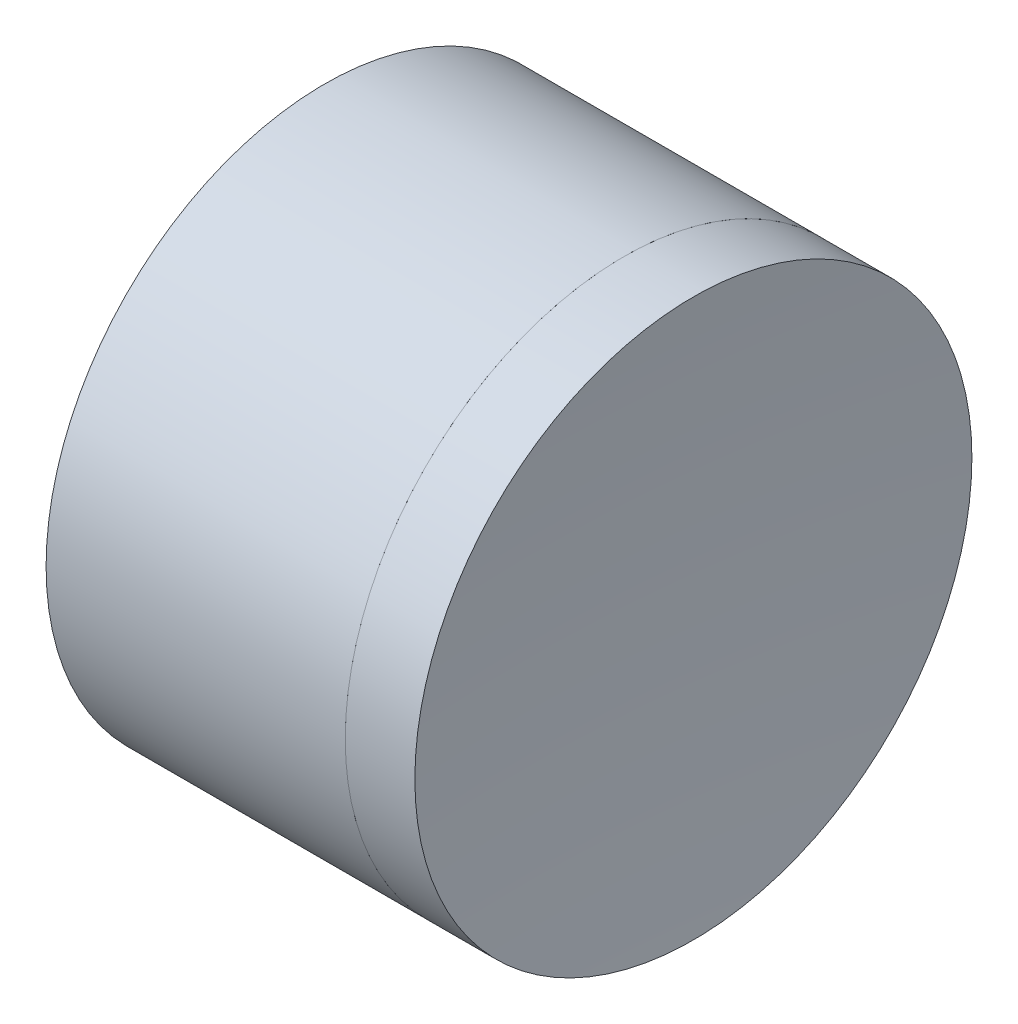
SolidWorks part; units mm, degrees
ref_plane "前视基准面" through (0, 0, 0) normal (0, 0, 1) x (1, 0, 0)
ref_plane "上视基准面" through (0, 0, 0) normal (0, 1, 0) x (1, 0, 0)
ref_plane "右视基准面" through (0, 0, 0) normal (1, 0, 0) x (0, 0, -1)
sketch "草图1" plane through (0, 0, 0) normal (0, 1, 0) x (1, 0, 0)
  line L0 (-0.8161, 0) -> (420.2002, 0) construction
  line L1 (226.8644, 12.5) -> (240.2901, 12.5)
  line L4 (226.8644, -12.5) -> (240.2901, -12.5)
  arc A0 (226.8644, -12.5) -> (226.8644, 12.5) centre (209.6921, 0) ccw
  arc A1 (240.2901, 12.5) -> (240.2901, -12.5) centre (252.1921, 0) ccw
  point P6 (230.9321, 0)
  point P8 (234.9321, 0)
  dimension "D3" = 12.5
  dimension "D4" = 4
  dimension "D1" = 21.24
  dimension "D5" = 17.26
  dimension "D2" = 12.5
revolve "旋转1" add sketch "草图1" angle 360 about L0
sketch "草图2" plane through (0, 0, 0) normal (0, 1, 0) x (1, 0, 0)
  line L2 (226.8644, 0) -> (249.4445, 0) construction
  line L3 (226.8644, -12.5) -> (226.8644, 12.5) construction
  line L6 (240.2901, 12.5) -> (243.4143, 12.5)
  line L7 (240.2901, -12.5) -> (243.4143, -12.5)
  arc A2 (240.2901, 12.5) -> (240.2901, -12.5) centre (252.1921, 0) ccw construction
  arc A3 (240.2901, 12.5) -> (240.2901, -12.5) centre (252.1921, 0) ccw
  arc A4 (243.4143, 12.5) -> (243.4143, -12.5) centre (405.1721, 0) ccw
  point P8 (234.9321, 0)
  point P9 (242.9321, 0)
  point P10 (249.4445, 0)
  dimension "D1" = 8
  dimension "D2" = 162.24
revolve "旋转3" add sketch "草图2" angle 360 about L2
